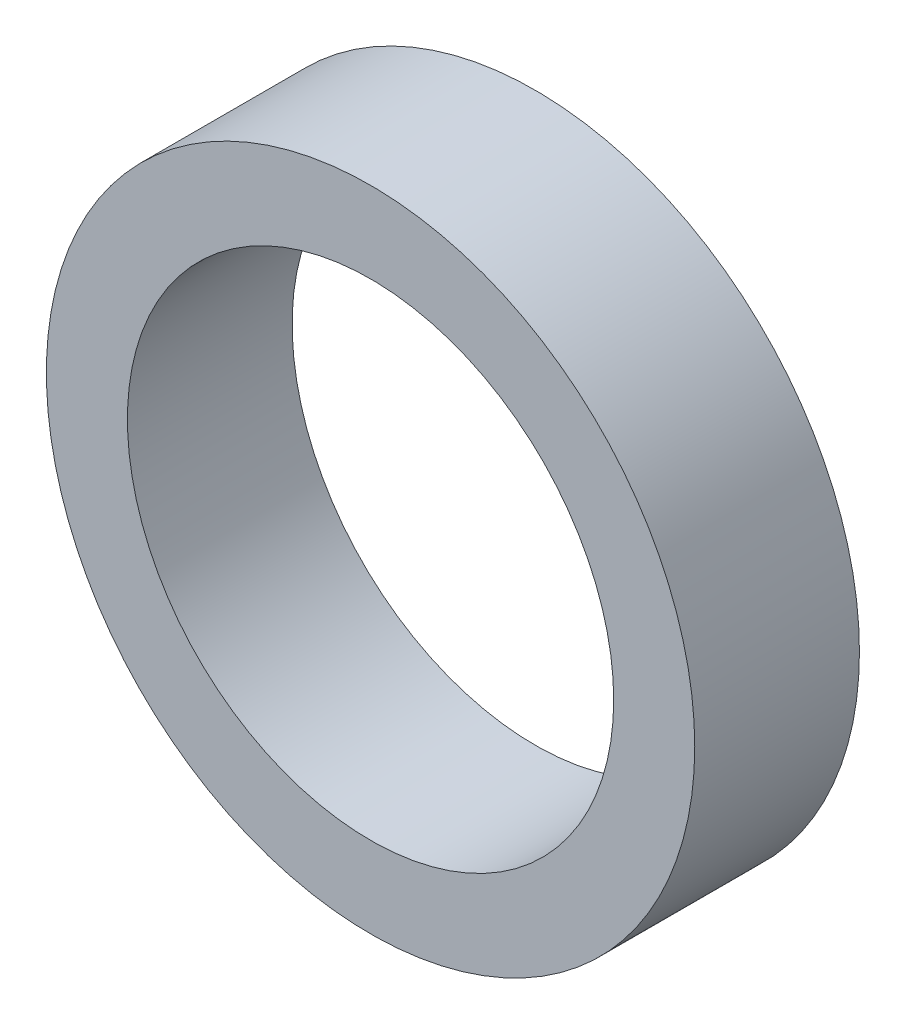
SolidWorks part; units mm, degrees
ref_plane "Front Plane" through (0, 0, 0) normal (0, 0, 1) x (1, 0, 0)
ref_plane "Top Plane" through (0, 0, 0) normal (0, 1, 0) x (1, 0, 0)
ref_plane "Right Plane" through (0, 0, 0) normal (1, 0, 0) x (0, 0, -1)
sketch "Sketch1" plane through (0, 0, 0) normal (0, 0, 1) x (1, 0, 0)
  circle A0 centre (0, 0) radius 1.5
  circle A1 centre (0, 0) radius 2
extrude "Extrude1" add sketch "Sketch1" along normal blind 1.016
